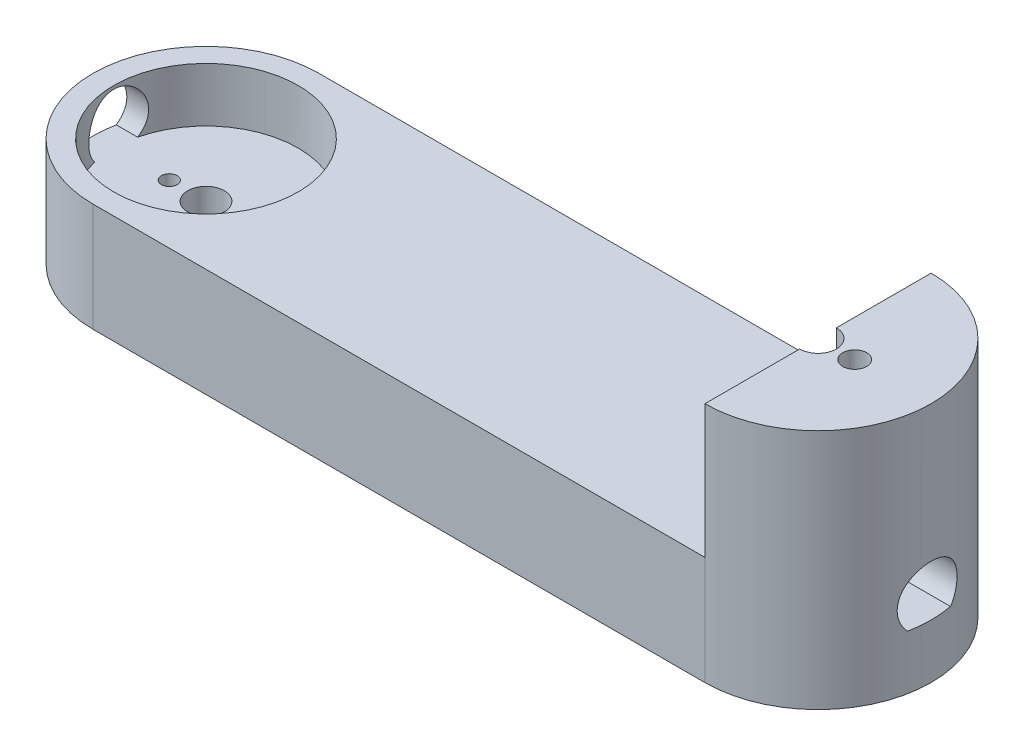
SolidWorks part; units mm, degrees
ref_plane "Front Plane" through (0, 0, 0) normal (0, 0, 1) x (1, 0, 0)
ref_plane "Top Plane" through (0, 0, 0) normal (0, 1, 0) x (1, 0, 0)
ref_plane "Right Plane" through (0, 0, 0) normal (1, 0, 0) x (0, 0, -1)
sketch "Sketch1" plane through (0, 0, 0) normal (0, 1, 0) x (1, 0, 0)
  line L0 (-58.41, 0) -> (58.41, 0) construction
  line L5 (-58.41, 21.59) -> (58.41, 21.59)
  line L6 (-58.41, -21.59) -> (58.41, -21.59)
  line L7 (-80, 59.4688) -> (-80, -43.591) construction
  line L8 (80, 48.0549) -> (80, -68.0864) construction
  line L9 (0, -55) -> (0, 55) construction
  arc A4 (-58.41, 21.59) -> (-58.41, -21.59) centre (-58.41, 0) ccw
  arc A5 (58.41, -21.59) -> (58.41, 21.59) centre (58.41, 0) ccw
  circle A6 centre (-58.41, 0) radius 3.5
  circle A8 centre (-51.41, 0) radius 1.498
  circle A9 centre (-65.41, 0) radius 1.498
  circle A10 centre (51.41, 0) radius 1.498
  circle A11 centre (65.41, 0) radius 1.498
  circle A12 centre (58.41, 0) radius 3.5
  point P2 (0, 0)
  point P19 (0, 0)
  dimension "D4" = 2.996
  dimension "D5" = 7
  dimension "D2" = 160
  dimension "D3" = 7
  dimension "D1" = 43.18
  dimension "D6" = 7
extrude "Boss-Extrude1" add sketch "Sketch1" along normal blind 20.7
sketch "Sketch2" plane through (0, 20.7, 0) normal (0, 1, 0) x (1, 0, 0)
  circle A0 centre (-58.41, 0) radius 17.6072
  dimension "D1" = 35.2145
extrude "Cut-Extrude1" cut sketch "Sketch2" against normal blind 10.35
sketch "Sketch3" plane through (0, 0, 0) normal (1, 0, 0) x (0, 0, -1)
  line L0 (0, 20.7) -> (0, 0) construction
  line L1 (21.59, 20.7) -> (-21.59, 20.7) construction
  line L2 (-21.59, 0) -> (21.59, 0) construction
  line L4 (4.0818, 10.35) -> (-4.0818, 10.35)
  arc A0 (4.0818, 10.35) -> (-4.0818, 10.35) centre (0, 14.35) ccw
  point P10 (0, 0)
  point P11 (0, 0)
  point P12 (0, 0)
  point P13 (0, 0)
  dimension "D1" = 11.43
  dimension "D2" = 6.35
  dimension "D3" = 10.35
extrude "Cut-Extrude2" cut sketch "Sketch3" against normal through all both and the other way through all
sketch "Sketch4" plane through (0, 20.7, 0) normal (0, 1, 0) x (1, 0, 0)
  line L0 (58.41, -21.59) -> (58.41, 21.59)
  arc A0 (58.41, -21.59) -> (58.41, 21.59) centre (58.41, 0) ccw construction
  arc A1 (58.41, -21.59) -> (58.41, 21.59) centre (58.41, 0) ccw
  circle A2 centre (65.41, 0) radius 1.498 construction
  circle A3 centre (65.41, 0) radius 1.498
extrude "Boss-Extrude2" add sketch "Sketch4" along normal blind 25.4
sketch "Sketch5" plane through (58.41, 0, 0) normal (-1, 0, 0) x (0, 0, 1)
  line L0 (0, 46.1) -> (0, 20.7) construction
  line L1 (-21.59, 46.1) -> (21.59, 46.1) construction
  line L2 (-3.5, 20.7) -> (3.5, 20.7) construction
  line L3 (0.9525, 22.6527) -> (-0.9525, 22.6527)
  line L4 (-0.9525, 22.6527) -> (-0.9525, 23.9227)
  line L5 (0.9525, 22.6527) -> (0.9525, 23.9227)
  arc A0 (0.9525, 23.9227) -> (-0.9525, 23.9227) centre (0, 33.4) ccw
  point P12 (0, 22.6527)
  dimension "D1" = 19.05
  dimension "D2" = 0.9525
  dimension "D3" = 1.27
extrude "Cut-Extrude3" cut sketch "Sketch5" against normal blind 8.89
sketch "Sketch6" plane through (0, 46.1, 0) normal (0, 1, 0) x (1, 0, 0)
  line L0 (58.41, 21.59) -> (58.41, -21.59) construction
  arc A0 (58.41, 3.5) -> (58.41, -3.5) centre (58.41, 0) ccw construction
  arc A1 (58.41, 3.5) -> (58.41, -3.5) centre (58.41, 0) ccw
  arc A2 (58.41, 3.5) -> (58.41, -3.5) centre (58.41, 0) cw
  line M2 (58.41, 21.59) -> (58.41, -21.59)
extrude "Cut-Extrude4" cut sketch "Sketch6" against normal up to surface (46.1 mm away) contours A1 M2 | A2 M2 up to face at (0, 0, 0)
sketch "Sketch7" plane through (0, 46.1, 0) normal (0, 1, 0) x (1, 0, 0)
  circle A0 centre (65.41, 0) radius 2.286
  dimension "D1" = 4.572
extrude "Cut-Extrude5" cut sketch "Sketch7" against normal up to surface (35.75 mm away) up to face at (-29.205, 10.35, 0)
